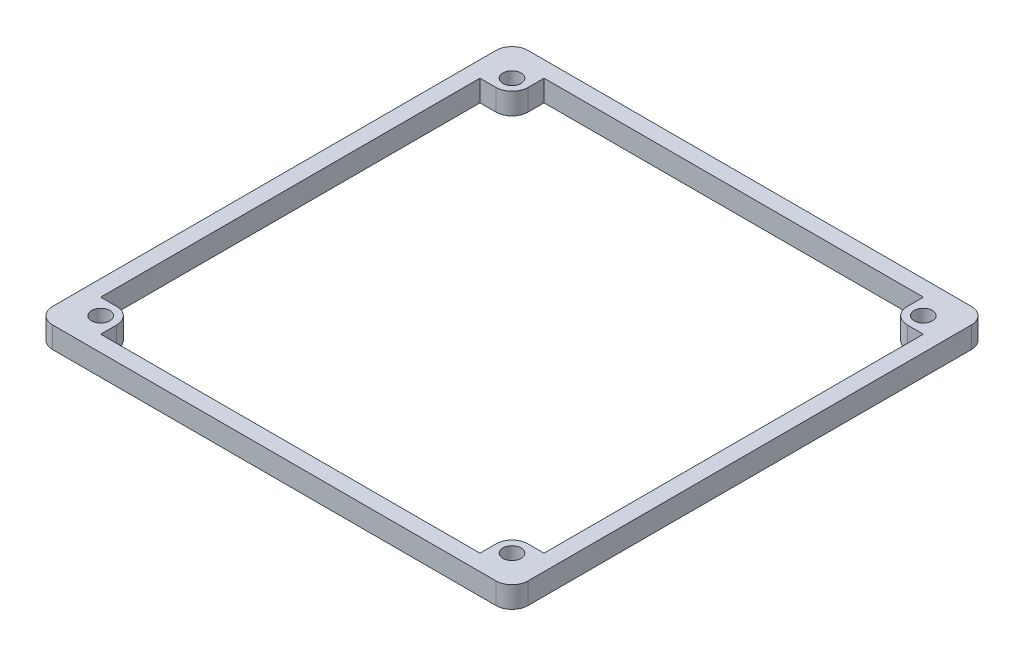
SolidWorks part; units mm, degrees
ref_plane "Front Plane" through (0, 0, 0) normal (0, 0, 1) x (1, 0, 0)
ref_plane "Top Plane" through (0, 0, 0) normal (0, 1, 0) x (1, 0, 0)
ref_plane "Right Plane" through (0, 0, 0) normal (1, 0, 0) x (0, 0, -1)
sketch "Sketch1" plane through (0, 0, 0) normal (0, 1, 0) x (1, 0, 0)
  line L0 (44.5, 89) -> (44.5, 0) construction
  line L1 (0, 0) -> (89, 0)
  line L2 (0, 0) -> (0, 89)
  line L3 (0, 89) -> (89, 89)
  line L4 (89, 0) -> (89, 89)
  line L5 (3, 3) -> (86, 3)
  line L6 (3, 3) -> (3, 86)
  line L7 (3, 86) -> (86, 86)
  line L8 (86, 3) -> (86, 86)
  dimension "D1" = 3
  dimension "D2" = 3
  dimension "D3" = 83
  dimension "D4" = 3
extrude "Boss-Extrude1" add sketch "Sketch1" along normal mid plane 4
sketch "Sketch4" plane through (0, -2, 0) normal (0, -1, 0) x (1, 0, 0)
  line L0 (80, -3) -> (86, -3)
  line L1 (3, -3) -> (9, -3)
  line L2 (3, -3) -> (3, -9)
  line L3 (3, -9) -> (9, -9)
  line L4 (9, -3) -> (9, -9)
  line L17 (80, -3) -> (80, -9)
  line L18 (80, -9) -> (86, -9)
  line L19 (86, -3) -> (86, -9)
  line L21 (80, -80) -> (86, -80)
  line L22 (80, -80) -> (80, -86)
  line L23 (80, -86) -> (86, -86)
  line L24 (86, -80) -> (86, -86)
  line L29 (3, -80) -> (9, -80)
  line L30 (3, -80) -> (3, -86)
  line L31 (3, -86) -> (9, -86)
  line L32 (9, -80) -> (9, -86)
  circle A0 centre (6, -6) radius 1.7
  circle A1 centre (83, -6) radius 1.7
  circle A2 centre (83, -83) radius 1.7
  circle A4 centre (6, -83) radius 1.7
  point P7 (6, -3)
  point P8 (9, -6)
  point P17 (83, -3)
  point P18 (86, -6)
  point P30 (83, -80)
  point P31 (86, -83)
  point P38 (6, -80)
  point P39 (9, -83)
  dimension "D1" = 3.4
  dimension "D4" = 3.4
  dimension "D7" = 3.4
  dimension "D10" = 3.4
  dimension "D2" = 6
  dimension "D3" = 6
  dimension "D5" = 6
  dimension "D6" = 6
  dimension "D8" = 6
  dimension "D9" = 6
  dimension "D11" = 6
  dimension "D12" = 6
extrude "Boss-Extrude3" add sketch "Sketch4" against normal blind 4
fillet "Fillet3" radius 3 4 edges at (9, 0, -80) (80, 0, -80) (9, 0, -9) (80, 0, -9)
fillet "Fillet4" radius 3 4 edges at (0, 0, -89) (0, 0, 0) (89, 0, -89) (89, 0, 0)
